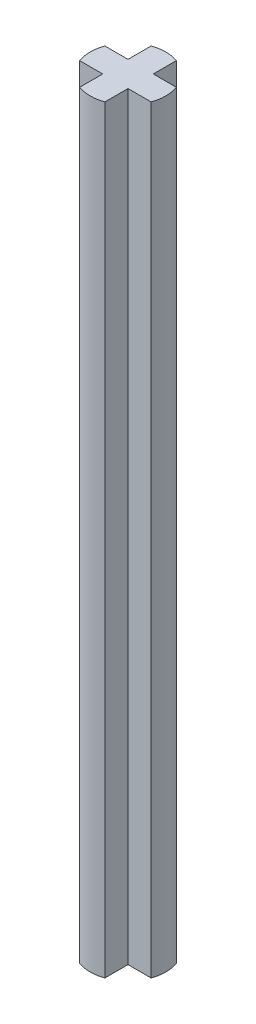
SolidWorks part; units mm, degrees
ref_plane "Front Plane" through (0, 0, 0) normal (0, 0, 1) x (1, 0, 0)
ref_plane "Top Plane" through (0, 0, 0) normal (0, 1, 0) x (1, 0, 0)
ref_plane "Right Plane" through (0, 0, 0) normal (1, 0, 0) x (0, 0, -1)
sketch "Sketch1" plane through (0, 0, 0) normal (0, 1, 0) x (1, 0, 0)
  line L1 (-1.5, -0.5) -> (1.5, -0.5)
  line L2 (-1.5, -0.5) -> (-1.5, 0.5)
  line L3 (-1.5, 0.5) -> (1.5, 0.5)
  line L4 (1.5, -0.5) -> (1.5, 0.5)
  line L5 (-1.5, -0.5) -> (1.5, 0.5) construction
  line L6 (-1.5, 0.5) -> (1.5, -0.5) construction
  line L7 (-0.5, -1.5) -> (0.5, -1.5)
  line L8 (-0.5, -1.5) -> (-0.5, 1.5)
  line L9 (-0.5, 1.5) -> (0.5, 1.5)
  line L10 (0.5, -1.5) -> (0.5, 1.5)
  line L11 (-0.5, -1.5) -> (0.5, 1.5) construction
  line L12 (-0.5, 1.5) -> (0.5, -1.5) construction
  point P0 (0, 0)
  point P6 (0, 0)
  dimension "D1" = 1
  dimension "D2" = 3
extrude "Boss-Extrude1" add sketch "Sketch1" along normal blind 30 contours L4 L3 L2 L1 | L10 L9 L8 L7
sketch "Sketch2" plane through (0, 30, 0) normal (0, 1, 0) x (1, 0, 0)
  circle A0 centre (0, 0) radius 1.5
extrude "Cut-Extrude1" cut sketch "Sketch2" against normal up to next (30 mm away) flip side to cut
